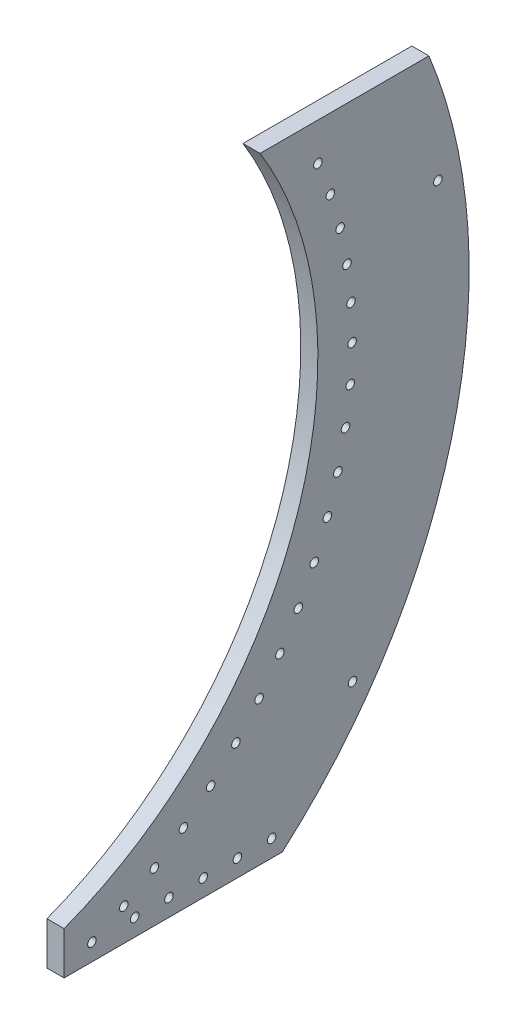
SolidWorks part; units mm, degrees
ref_plane "Front Plane" through (0, 0, 0) normal (0, 0, 1) x (1, 0, 0)
ref_plane "Top Plane" through (0, 0, 0) normal (0, 1, 0) x (1, 0, 0)
ref_plane "Right Plane" through (0, 0, 0) normal (1, 0, 0) x (0, 0, -1)
sketch "Sketch1" plane through (0, 0, 0) normal (1, 0, 0) x (0, 0, -1)
  line L0 (0, 609.6) -> (323.85, 609.6)
  line L1 (323.85, 609.6) -> (323.85, 0)
  line L2 (323.85, 0) -> (0, 0)
  line L3 (0, 609.6) -> (0, 577.85)
  line L4 (0, 0) -> (0, 31.75)
  arc A1 (0, 577.85) -> (0, 31.75) centre (-103.7599, 304.8) cw
  dimension "D4" = 292.1
  dimension "D1" = 609.6
  dimension "D2" = 323.85
  dimension "D3" = 546.1
extrude "Boss-Extrude1" add sketch "Sketch1" along normal blind 12.7
sketch "Sketch2" plane through (12.7, 0, 0) normal (1, 0, 0) x (0, 0, -1)
  line L0 (323.85, 0) -> (323.85, 609.6) construction
  line L1 (0, 609.6) -> (323.85, 609.6)
  line L2 (0, 609.6) -> (0, 457.2)
  line L3 (0, 457.2) -> (323.85, 457.2)
  line L4 (323.85, 609.6) -> (323.85, 457.2)
  dimension "D1" = 152.4
extrude "Cut-Extrude1" cut sketch "Sketch2" against normal blind 12.7
sketch "Sketch3" plane through (12.7, 0, 0) normal (1, 0, 0) x (0, 0, -1)
  circle A0 centre (-103.7599, 304.8) radius 317.5
hole_wizard "1/4 (0.25) Diameter Hole1" positions "Sketch6" profile "Sketch7" hole size "1/4" standard "ANSI Inch" end condition through all
sketch "Sketch6" plane through (12.7, 0, 0) normal (1, 0, 0) x (0, 0, -1)
  line L0 (0, 0) -> (323.85, 0) construction
  point P0 (20.6742, 12.7)
  point P14 (44.3706, 23.9734)
  point P15 (67.0552, 37.165)
  point P16 (88.5729, 52.1849)
  point P17 (108.7768, 68.9305)
  point P18 (127.5288, 87.2872)
  point P19 (144.7009, 107.1298)
  point P20 (160.1757, 128.3227)
  point P21 (173.8477, 150.7211)
  point P22 (185.6232, 174.172)
  point P23 (195.422, 198.5152)
  point P24 (203.1771, 223.5844)
  point P25 (208.8355, 249.2085)
  point P26 (212.3585, 275.2123)
  point P27 (213.7221, 301.4182)
  point P28 (212.917, 327.6472)
  point P29 (209.9487, 353.7201)
  point P30 (204.8375, 379.4589)
  point P31 (197.6182, 404.6876)
  point P32 (188.3401, 429.2341)
  dimension "D1" = 12.7
  dimension "D2" = 317.5
  dimension "D3" = 20
sketch "Sketch7" plane through (12.7, 12.7, -20.6742) normal (0, 1, 0) x (0, 0, -1)
  line L0 (0, 0) -> (0, 12.7)
  line L1 (0, 12.7) -> (3.175, 12.7)
  line L2 (3.175, 12.7) -> (3.175, 0)
  line L5 (3.175, 0) -> (0, 0)
  line L11 (0, -6.35) -> (0, 107.95) construction
  dimension "Thru Hole Dia." = 6.35
  dimension "Thru Hole Depth" = 12.7
sketch "Sketch8" plane through (12.7, 0, 0) normal (1, 0, 0) x (0, 0, -1)
  line L0 (0, 0) -> (323.85, 0) construction
  line L1 (145.4321, 457.2) -> (323.85, 457.2) construction
  line L2 (270.7608, 457.2) -> (323.85, 457.2)
  line L3 (323.85, 457.2) -> (323.85, 0)
  line L4 (323.85, 0) -> (161.925, 0)
  arc A0 (161.925, 0) -> (270.7608, 457.2) centre (-103.7599, 304.8) ccw
extrude "Cut-Extrude2" cut sketch "Sketch8" against normal through all
sketch "Sketch9" plane through (12.7, 0, 0) normal (1, 0, 0) x (0, 0, -1)
  circle A0 centre (214.0657, 83.3797) radius 3.175
  circle A1 centre (277.3838, 373.8621) radius 3.175
  arc A2 (161.925, 0) -> (270.7608, 457.2) centre (-103.7599, 304.8) ccw construction
  point P4 (0, 0)
  point P5 (220.6116, 79.7071)
  point P6 (0, 0)
  point P7 (0, 0)
  point P8 (217.3204, 81.1123)
  point P12 (283.5346, 269.1562)
  point P13 (283.2219, 284.9211)
  point P14 (283.0237, 258.5919)
  point P15 (274.0736, 373.2623)
  point P16 (0, 0)
  dimension "D1" = 387.35
  dimension "D2" = 387.35
extrude "Cut-Extrude3" cut sketch "Sketch9" against normal through all
sketch "Sketch10" plane through (0, 0, 0) normal (-1, 0, 0) x (0, 0, 1)
  line L0 (0, 0) -> (-161.925, 0) construction
  circle A0 centre (-154.038, 12.7) radius 3.175
  point P2 (0, 0)
  point P3 (0, 0)
  point P4 (-154.038, 8.563)
  dimension "D1" = 12.7
extrude "Cut-Extrude4" cut sketch "Sketch10" against normal through all
pattern_linear "LPattern1" count 5 spacing 25.4 along (0, 0, 1) of "Cut-Extrude4"
